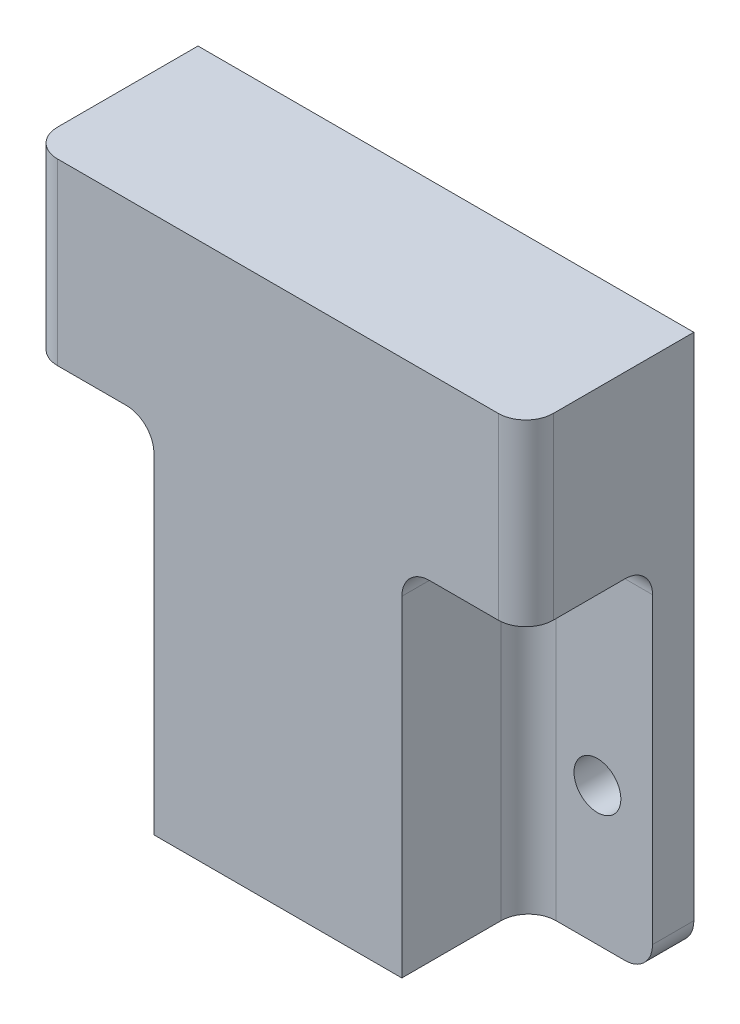
SolidWorks part; units mm, degrees
material "ABS"
ref_plane "Ebene vorne" through (0, 0, 0) normal (0, 0, 1) x (1, 0, 0)
ref_plane "Ebene oben" through (0, 0, 0) normal (0, 1, 0) x (1, 0, 0)
ref_plane "Ebene rechts" through (0, 0, 0) normal (1, 0, 0) x (0, 0, -1)
sketch "Skizze1" plane through (0, 0, 0) normal (0, 0, 1) x (1, 0, 0)
  line L1 (0, 0) -> (-18, 0)
  line L2 (0, 0) -> (0, 10)
  line L3 (0, 10) -> (-18, 10)
  line L4 (-18, 0) -> (-18, 10)
  dimension "D1" = 10
  dimension "D2" = 18
extrude "Aufsatz-Linear austragen1" add sketch "Skizze1" along normal blind 3
hole_wizard "Durchgangsloch für M31" positions "Skizze3" profile "Skizze4" hole size "M3" standard "DIN" end condition through all
sketch "Skizze3" plane through (0, 0, 3) normal (0, 0, 1) x (1, 0, 0)
  line L0 (-18, 0) -> (0, 0) construction
  line L3 (0, 0) -> (0, 10) construction
  point P0 (-14, 0)
  dimension "D1" = 14
sketch "Skizze4" plane through (-14, 0, 3) normal (1, 0, 0) x (0, -1, 0)
  line L0 (0, 0) -> (0, 3)
  line L1 (0, 3) -> (1.7, 3)
  line L2 (1.7, 3) -> (1.7, 0)
  line L5 (1.7, 0) -> (0, 0)
  line L11 (0, -6.35) -> (0, 107.95) construction
  dimension "Bohrerdurchmesser" = 3.4
  dimension "Bohrungstiefe" = 3
sketch "Skizze5" plane through (0, 0, 0) normal (0, 0, -1) x (-1, 0, 0)
  line L1 (0, 0) -> (8, 0)
  line L2 (0, 0) -> (0, 3)
  line L3 (0, 3) -> (8, 3)
  line L4 (8, 0) -> (8, 3)
  dimension "D1" = 8
  dimension "D2" = 3
extrude "Aufsatz-Linear austragen2" add sketch "Skizze5" along normal blind 3
sketch "Skizze7" plane through (0, 10, 0) normal (0, 1, 0) x (1, 0, 0)
  line L0 (-6.5, -3) -> (-6.5, -9)
  line L1 (0, -3) -> (-18, -3) construction
  line L2 (-6.5, -9) -> (0, -9)
  line L3 (0, -9) -> (0, -12.2)
  line L4 (0, -12.2) -> (-9, -12.2)
  line L5 (-9, -12.2) -> (-9, -3)
  line L6 (-9, -3) -> (-6.5, -3)
  line L7 (0, -3) -> (0, 0) construction
  dimension "D1" = 2.5
  dimension "D2" = 3.2
  dimension "D3" = 6.5
  dimension "D4" = 6
extrude "Aufsatz-Linear austragen3" add sketch "Skizze7" against normal up to surface (10 mm away) up to face at (-16.85, 0, 1.5)
mirror "Spiegeln2" about plane through (0, 0, 3) normal (0, 1, 0) of bodies 104 105
sketch "Skizze16" plane through (0, 10, 0) normal (0, 1, 0) x (1, 0, 0)
  line L10 (0, 0) -> (-18, 0)
  line L11 (-18, 0) -> (-18, -3)
  line L12 (-18, -3) -> (-9, -3)
  line L13 (-9, -3) -> (-9, -12.2)
  line L14 (-9, -12.2) -> (0, -12.2)
  line L15 (0, -12.2) -> (0, -9)
  line L16 (0, -9) -> (-6.5, -9)
  line L17 (-6.5, -9) -> (-6.5, -3)
  line L18 (-6.5, -3) -> (0, -3)
  line L19 (0, -3) -> (0, 0)
  line L20 (0, 0) -> (-18, 0)
  line L21 (-18, 0) -> (-18, -3)
  line L22 (-18, -3) -> (-9, -3)
  line L23 (-9, -3) -> (-9, -12.2)
  line L24 (-9, -12.2) -> (0, -12.2)
  line L25 (0, -12.2) -> (0, -9)
  line L26 (0, -9) -> (-6.5, -9)
  line L27 (-6.5, -9) -> (-6.5, -3)
  line L28 (-6.5, -3) -> (0, -3)
  line L29 (0, -3) -> (0, 0)
  dimension "D1" = 0
extrude "Aufsatz-Linear austragen7" add sketch "Skizze16" along normal blind 9
hole_wizard "Stirnsenkung für M2 Flachkopfschraube mit Schlitz1" [suppressed] positions "Skizze9" profile "Skizze11" counterbore size "M2" standard "DIN"
sketch "Skizze9" plane through (0, 0, 12.2) normal (0, 0, 1) x (1, 0, 0)
  line L1 (0, -10) -> (0, 15) construction
  line L2 (-9, 15) -> (0, 15) construction
  point P0 (-3.25, 10)
  dimension "D1" = 5
  dimension "D2" = 3.25
sketch "Skizze11" plane through (-3.25, 10, 12.2) normal (1, 0, 0) x (0, -1, 0)
  line L0 (0, 0) -> (0, 15.2)
  line L1 (0, 15.2) -> (1.2, 15.2)
  line L3 (1.2, 15.2) -> (1.2, 2.1)
  line L4 (1.2, 2.1) -> (2.5, 2.1)
  line L5 (2.5, 2.1) -> (2.5, 0)
  line L7 (2.5, 0) -> (0, 0)
  line L11 (0, -6.35) -> (0, 107.95) construction
  dimension "Bohrerdurchmesser" = 2.4
  dimension "Bohrungstiefe" = 15.2
  dimension "Senkdurchmesser2" = 5
  dimension "Senktiefe2" = 2.1
sketch "Skizze12" [suppressed] plane through (0, 0, 0) normal (0, 0, -1) x (-1, 0, 0)
  line L1 (5.5594, 10) -> (4.4047, 12)
  line L2 (4.4047, 12) -> (2.0953, 12)
  line L3 (2.0953, 12) -> (0.9406, 10)
  line L4 (0.9406, 10) -> (2.0953, 8)
  line L5 (2.0953, 8) -> (4.4047, 8)
  line L6 (4.4047, 8) -> (5.5594, 10)
  line L7 (0, 15) -> (18, 15) construction
  circle A0 centre (3.25, 10) radius 2 construction
  dimension "D1" = 4
extrude "Schnitt-Linear austragen1" [suppressed] cut sketch "Skizze12" against normal blind 1.5
sketch "Skizze19" plane through (0, 0, 3) normal (0, 0, 1) x (1, 0, 0)
  line L0 (0, -10) -> (0, 19) construction
  line L1 (-18, 19) -> (0, 19)
  line L2 (-18, 19) -> (-18, 16)
  line L3 (-18, 16) -> (0, 16)
  line L4 (0, 19) -> (0, 16)
  dimension "D1" = 3
extrude "Aufsatz-Linear austragen8" add sketch "Skizze19" along normal up to surface (9.2 mm away) up to face at (-4.5, 4.5, 12.2)
fillet "Verrundung1" radius 2 4 edges at (-9, 16, 7.6) (-13.5, 16, 3) (-18, 17.5, 12.2) (-9, 3, 3)
fillet "Verrundung2" [suppressed] radius 2
fillet "Verrundung3" radius 2 1 edges at (-18, -10, 1.5)
mirror "Spiegeln1" about plane through (0, 0, 3) normal (-1, 0, 0) of bodies 113 104
sketch "Skizze20" plane through (0, 19, 0) normal (0, 1, 0) x (1, 0, 0)
  line L4 (-18, 0) -> (-18, -10.2)
  line L5 (-16, -12.2) -> (16, -12.2)
  line L6 (18, -10.2) -> (18, 0)
  line L7 (18, 0) -> (-18, 0)
  line L8 (-18, 0) -> (-18, -10.2)
  line L9 (-16, -12.2) -> (16, -12.2)
  line L10 (18, -10.2) -> (18, 0)
  line L11 (18, 0) -> (-18, 0)
  arc A2 (-18, -10.2) -> (-16, -12.2) centre (-16, -10.2) ccw
  arc A3 (16, -12.2) -> (18, -10.2) centre (16, -10.2) ccw
  arc A4 (-18, -10.2) -> (-16, -12.2) centre (-16, -10.2) ccw
  arc A5 (16, -12.2) -> (18, -10.2) centre (16, -10.2) ccw
  dimension "D1" = 0
extrude "Aufsatz-Linear austragen9" add sketch "Skizze20" along normal blind 10
